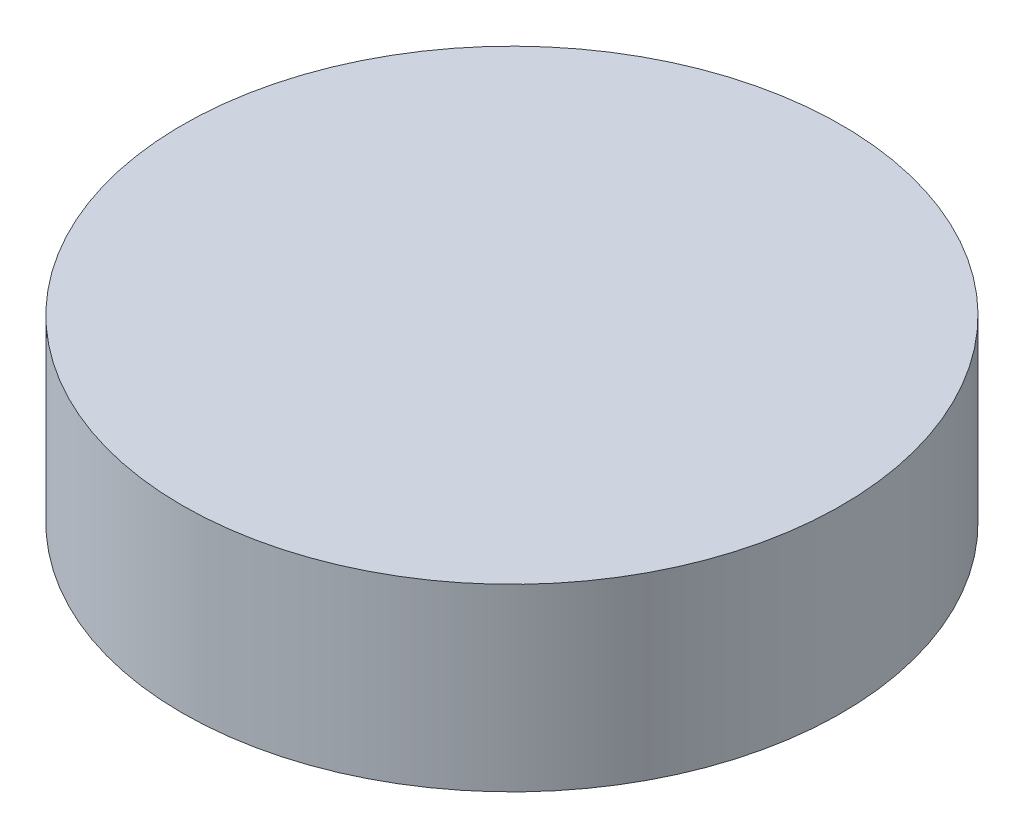
SolidWorks part; units mm, degrees
ref_plane "Front Plane" through (0, 0, 0) normal (0, 0, 1) x (1, 0, 0)
ref_plane "Top Plane" through (0, 0, 0) normal (0, 1, 0) x (1, 0, 0)
ref_plane "Right Plane" through (0, 0, 0) normal (1, 0, 0) x (0, 0, -1)
sketch "Sketch1" plane through (0, 0, 0) normal (0, 1, 0) x (1, 0, 0)
  circle A0 centre (0, 0) radius 11
  dimension "D1" = 22
extrude "Boss-Extrude1" add sketch "Sketch1" along normal blind 6
